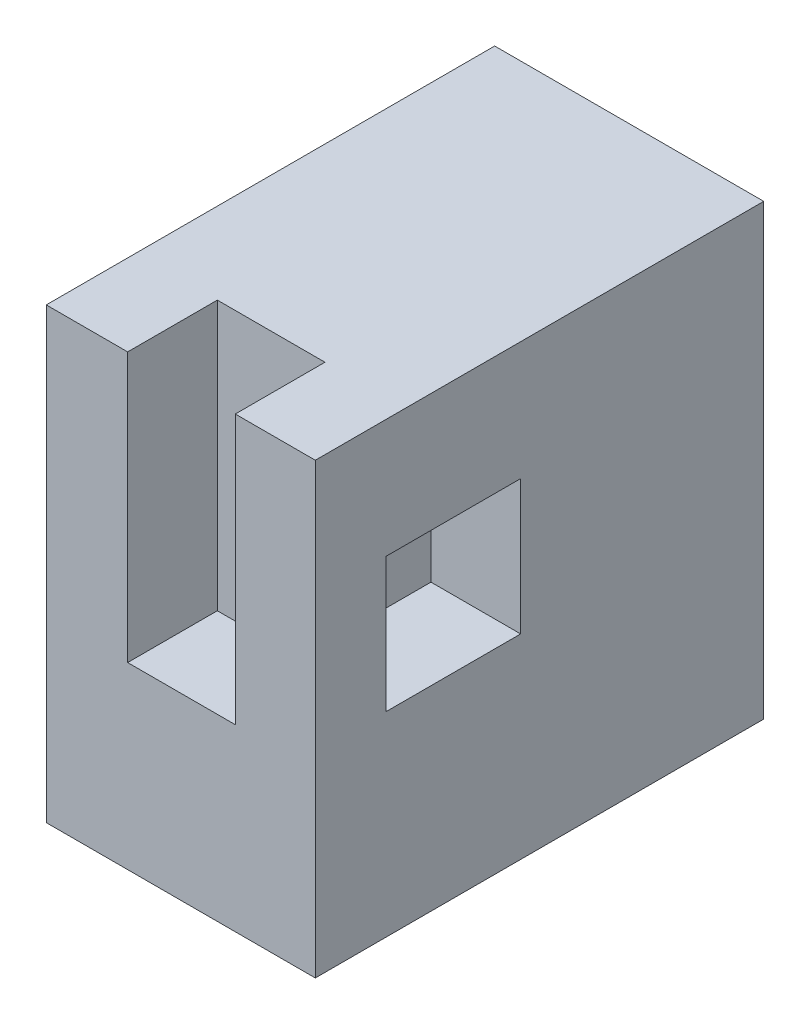
SolidWorks part; units mm, degrees
ref_plane "Plan de face" through (0, 0, 0) normal (0, 0, 1) x (1, 0, 0)
ref_plane "Plan de dessus" through (0, 0, 0) normal (0, 1, 0) x (1, 0, 0)
ref_plane "Plan de droite" through (0, 0, 0) normal (1, 0, 0) x (0, 0, -1)
sketch "Esquisse1" plane through (0, 0, 0) normal (0, 0, 1) x (1, 0, 0)
  line L1 (-77.2403, 9.0886) -> (-47.2403, 9.0886)
  line L2 (-77.2403, 9.0886) -> (-77.2403, -40.9114)
  line L3 (-77.2403, -40.9114) -> (-47.2403, -40.9114)
  line L4 (-47.2403, 9.0886) -> (-47.2403, -40.9114)
  dimension "D1" = 30
  dimension "D2" = 50
extrude "Boss.-Extru.1" add sketch "Esquisse1" along normal blind 50
sketch "Esquisse2" plane through (0, 0, 50) normal (0, 0, 1) x (1, 0, 0)
  line L0 (-47.2403, 9.0886) -> (-77.2403, 9.0886) construction
  line L1 (-68.1653, 9.0886) -> (-56.1653, 9.0886)
  line L2 (-68.1653, 9.0886) -> (-68.1653, -20.9114)
  line L3 (-68.1653, -20.9114) -> (-56.1653, -20.9114)
  line L4 (-56.1653, 9.0886) -> (-56.1653, -20.9114)
  dimension "D1" = 12
  dimension "D2" = 30
extrude "Enlèv. mat.-Extru.1" cut sketch "Esquisse2" against normal blind 10
sketch "Esquisse4" plane through (-47.2403, 0, 0) normal (1, 0, 0) x (0, 0, -1)
  line L1 (-42.1045, -19.1331) -> (-27.1045, -19.1331)
  line L2 (-42.1045, -19.1331) -> (-42.1045, -4.1331)
  line L3 (-42.1045, -4.1331) -> (-27.1045, -4.1331)
  line L4 (-27.1045, -19.1331) -> (-27.1045, -4.1331)
  dimension "D1" = 15
  dimension "D2" = 15
extrude "Enlèv. mat.-Extru.2" cut sketch "Esquisse4" against normal blind 10
